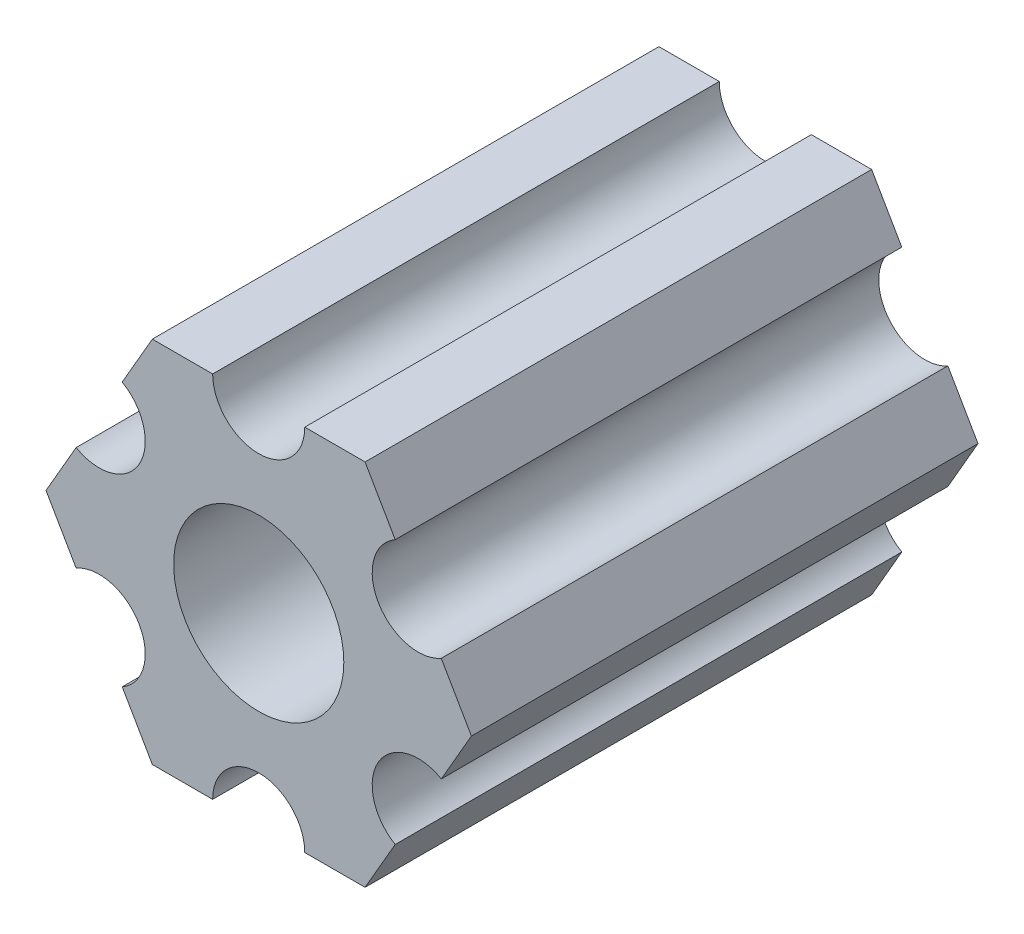
SolidWorks part; units mm, degrees
material "6061 Alloy"
ref_plane "Front Plane" through (0, 0, 0) normal (0, 0, 1) x (1, 0, 0)
ref_plane "Top Plane" through (0, 0, 0) normal (0, 1, 0) x (1, 0, 0)
ref_plane "Right Plane" through (0, 0, 0) normal (1, 0, 0) x (0, 0, -1)
ref_plane "Plane1" through (0, 0, 0) normal (0, 0, -1) x (-1, 0, 0)
sketch "Sketch1" plane through (0, 0, 0) normal (0, 0, -1) x (-1, 0, 0)
  line L0 (-4.7055, -4.5498) -> (-3.6662, -6.35)
  line L1 (-3.6662, -6.35) -> (-1.5875, -6.35)
  line L2 (1.5875, -6.35) -> (3.6662, -6.35)
  line L3 (3.6662, -6.35) -> (4.7055, -4.5498)
  line L4 (6.293, -1.8002) -> (7.3323, 0)
  line L5 (7.3323, 0) -> (6.293, 1.8002)
  line L6 (4.7055, 4.5498) -> (3.6662, 6.35)
  line L7 (3.6662, 6.35) -> (1.5875, 6.35)
  line L8 (-1.5875, 6.35) -> (-3.6662, 6.35)
  line L9 (-3.6662, 6.35) -> (-4.7055, 4.5498)
  line L10 (-6.293, 1.8002) -> (-7.3323, 0)
  line L11 (-7.3323, 0) -> (-6.293, -1.8002)
  circle A0 centre (0, 0) radius 2.9337
  arc A1 (-6.293, -1.8002) -> (-4.7055, -4.5498) centre (-5.4993, -3.175) cw
  arc A2 (-1.5875, -6.35) -> (1.5875, -6.35) centre (0, -6.35) cw
  arc A3 (4.7055, -4.5498) -> (6.293, -1.8002) centre (5.4993, -3.175) cw
  arc A4 (6.293, 1.8002) -> (4.7055, 4.5498) centre (5.4993, 3.175) cw
  arc A5 (1.5875, 6.35) -> (-1.5875, 6.35) centre (0, 6.35) cw
  arc A6 (-4.7055, 4.5498) -> (-6.293, 1.8002) centre (-5.4993, 3.175) cw
  dimension "D1" = 5.8674
  dimension "D2" = 1.5875
  dimension "D3" = 5.4993
  dimension "D4" = 6.293
extrude "Boss-Extrude1" add sketch "Sketch1" against normal blind 17.4625
